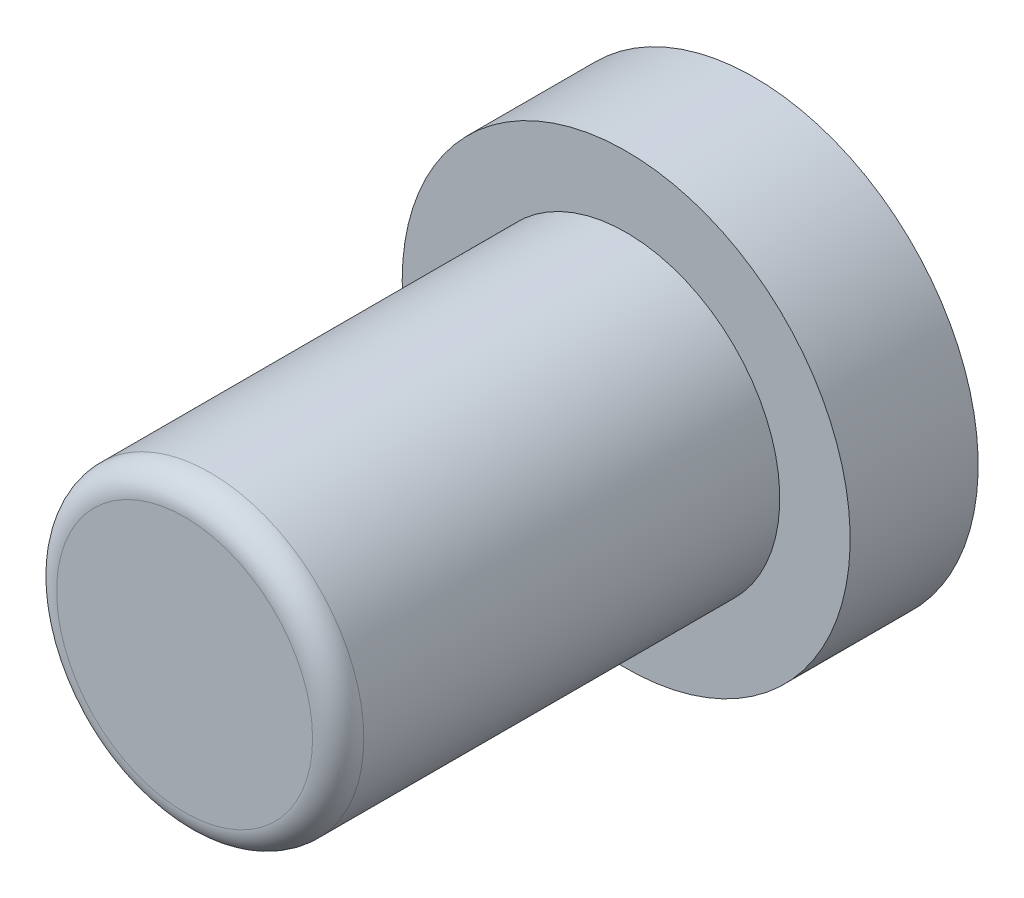
SolidWorks part; units mm, degrees
ref_plane "Front Plane" through (0, 0, 0) normal (0, 0, 1) x (1, 0, 0)
ref_plane "Top Plane" through (0, 0, 0) normal (0, 1, 0) x (1, 0, 0)
ref_plane "Right Plane" through (0, 0, 0) normal (1, 0, 0) x (0, 0, -1)
sketch "Sketch1" plane through (0, 0, 0) normal (0, 0, 1) x (1, 0, 0)
  circle A0 centre (0, 0) radius 4.8
  dimension "D1" = 9.6
extrude "Boss-Extrude1" add sketch "Sketch1" along normal mid plane 17.8
fillet "Fillet1" radius 0.8 1 edges at (4.8, 0, 8.9)
sketch "Sketch2" plane through (0, 0, -8.9) normal (0, 0, -1) x (-1, 0, 0)
  circle A0 centre (0, 0) radius 7
  dimension "D1" = 14
extrude "Boss-Extrude2" add sketch "Sketch2" against normal blind 4
